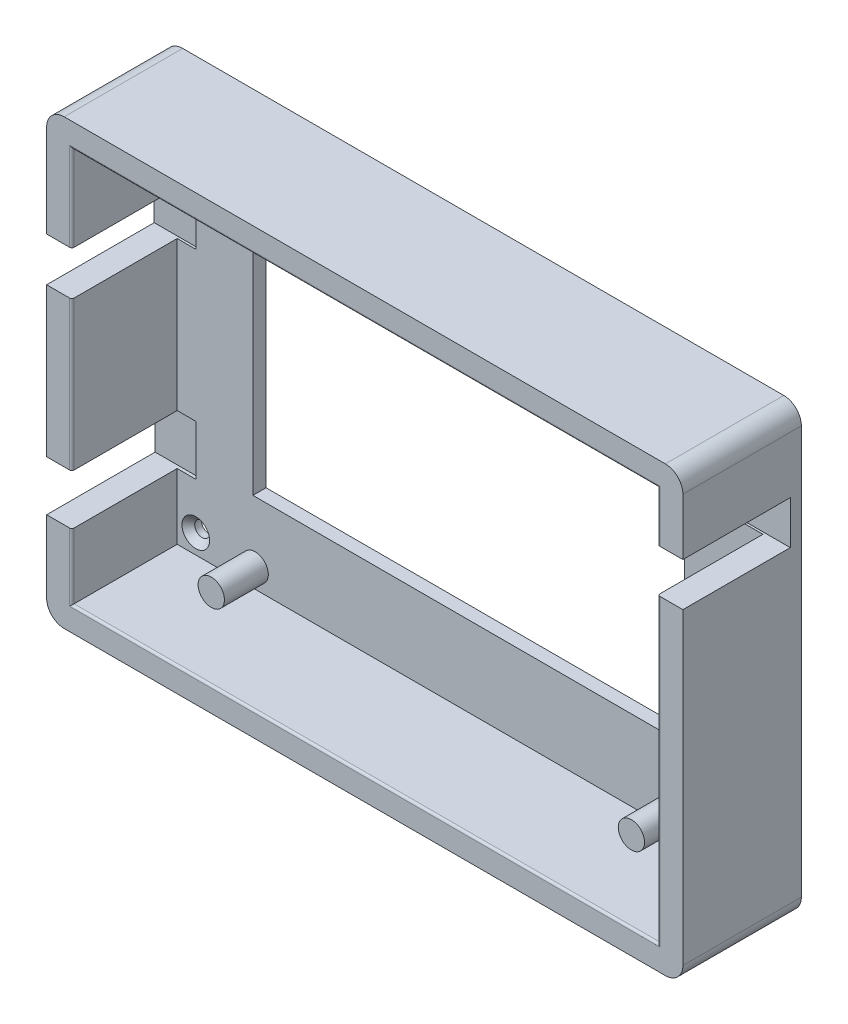
SolidWorks part; units mm, degrees
material "Caoutchouc"
ref_plane "Plan de face" through (0, 0, 0) normal (0, 0, 1) x (1, 0, 0)
ref_plane "Plan de dessus" through (0, 0, 0) normal (0, 1, 0) x (1, 0, 0)
ref_plane "Plan de droite" through (0, 0, 0) normal (1, 0, 0) x (0, 0, -1)
sketch "Esquisse1" plane through (0, 0, 0) normal (0, 0, 1) x (1, 0, 0)
  line L0 (66.75, 90) -> (66.75, 0) construction
  line L1 (0, 0) -> (133.5, 0)
  line L2 (0, 0) -> (0, 90)
  line L3 (0, 90) -> (133.5, 90)
  line L4 (133.5, 0) -> (133.5, 90)
  line L5 (0, 45) -> (133.5, 45) construction
  dimension "D1" = 133.5
  dimension "D2" = 90
sketch "EsquisseExterieur" plane through (0, 0, 0) normal (0, 0, 1) x (1, 0, 0)
  line L0 (66.75, 90) -> (66.75, 0) construction
  line L1 (-1.75, -5.5) -> (135.25, -5.5)
  line L2 (-5.75, -1.5) -> (-5.75, 91.5)
  line L3 (-1.75, 95.5) -> (135.25, 95.5)
  line L4 (139.25, -1.5) -> (139.25, 91.5)
  line L5 (-5.75, -5.5) -> (139.25, 95.5) construction
  line L6 (-5.75, 95.5) -> (139.25, -5.5) construction
  arc A0 (-1.75, -5.5) -> (-5.75, -1.5) centre (-1.75, -1.5) cw
  arc A1 (135.25, -5.5) -> (139.25, -1.5) centre (135.25, -1.5) ccw
  arc A2 (135.25, 95.5) -> (139.25, 91.5) centre (135.25, 91.5) cw
  arc A3 (-5.75, 91.5) -> (-1.75, 95.5) centre (-1.75, 91.5) cw
  point P0 (66.75, 45)
  dimension "D3" = 4
  dimension "D1" = 145
  dimension "D2" = 101
extrude "Boss.-Extru.1" add sketch "EsquisseExterieur" against normal blind 8 and the other way blind 19
extrude "Enlèv. mat.-Extru.1" cut sketch "Esquisse1" against normal blind 5 and the other way blind 47
hole_wizard "Fraisage pour vis à tête fraisée M32" positions "Esquisse6" profile "Esquisse5" countersink size "M3" standard "ISO"
sketch "Esquisse6" plane through (0, 0, -5) normal (0, 0, 1) x (1, 0, 0)
  point P0 (4.1451, 84.4434)
  point P2 (127.1274, 84.4434)
  point P4 (127.1274, 4.4159)
  point P6 (4.241, 4.4159)
sketch "Esquisse5" plane through (4.1451, 84.4434, -5) normal (1, 0, 0) x (0, -1, 0)
  line L0 (0, 0) -> (0, 6.0215)
  line L1 (0, 6.0215) -> (1.7, 5)
  line L2 (1.7, 5) -> (1.7, 1.45)
  line L3 (1.7, 1.45) -> (3.15, 0)
  line L5 (3.15, 0) -> (0, 0)
  line L6 (-1.7, 1.45) -> (-3.15, 0) construction
  line L10 (0, 6.0215) -> (-1.7, 5) construction
  line L11 (0, -6.35) -> (0, 107.95) construction
  dimension "Diamètre du perçage" = 3.4
  dimension "Profondeur du perçage" = 5
  dimension "Diamètre du fraisage entrant" = 6.3
  dimension "Angle du fraisage entrant" = 90
  dimension "Angle de pointe" = 118
sketch "Esquisse7" plane through (-5.75, 0, 0) normal (-1, 0, 0) x (0, 0, 1)
  line L0 (19, 91.5) -> (19, -1.5) construction
  line L1 (19, 70.3576) -> (-5.5113, 70.3576)
  line L2 (19, 70.3576) -> (19, 60.349)
  line L3 (19, 60.349) -> (-5.5113, 60.349)
  line L4 (-5.5113, 70.3576) -> (-5.5113, 60.349)
  point P0 (-1.0067, 57.9518)
  point P1 (-1.2778, 72.7474)
extrude "Enlèv. mat.-Extru.2" cut sketch "Esquisse7" against normal blind 10
sketch "Esquisse8" plane through (-5.75, 0, 0) normal (-1, 0, 0) x (0, 0, 1)
  line L0 (19, 60.349) -> (19, -1.5) construction
  line L1 (19, 26.3973) -> (-5.7237, 26.3973)
  line L2 (19, 26.3973) -> (19, 14.9604)
  line L3 (19, 14.9604) -> (-5.7237, 14.9604)
  line L4 (-5.7237, 26.3973) -> (-5.7237, 14.9604)
extrude "Enlèv. mat.-Extru.3" cut sketch "Esquisse8" against normal blind 10
sketch "Esquisse9" plane through (139.25, 0, 0) normal (1, 0, 0) x (0, 0, -1)
  line L0 (-19, -1.5) -> (-19, 91.5) construction
  line L1 (-19, 78.6074) -> (5.4787, 78.6074)
  line L2 (-19, 78.6074) -> (-19, 68.7301)
  line L3 (-19, 68.7301) -> (5.4787, 68.7301)
  line L4 (5.4787, 78.6074) -> (5.4787, 68.7301)
extrude "Enlèv. mat.-Extru.4" cut sketch "Esquisse9" against normal blind 10
fillet "Congé1" radius 0.5 7 edges at (133.5, 34.365, 19) (133.5, 84.3037, 19) (0, 80.1788, 19) (0, 43.3731, 19) (0, 7.4802, 19) (66.75, 0, 19) (66.75, 90, 19)
sketch "Esquisse10" plane through (0, 0, -5) normal (0, 0, 1) x (1, 0, 0)
  line L0 (4.1451, 84.4434) -> (127.1274, 84.4434) construction
  line L1 (4.241, 4.4159) -> (127.1274, 4.4159) construction
  line L2 (65.6363, 84.4434) -> (65.6842, 4.4159) construction
  line L3 (4.1451, 84.4434) -> (17.7708, 84.4434) construction
  line L4 (127.1274, 84.4434) -> (113.5135, 84.4434) construction
  line L5 (17.7708, 84.4434) -> (17.7708, 4.4159) construction
  line L6 (113.5135, 84.4434) -> (113.5135, 4.4159) construction
  circle A0 centre (17.7708, 84.4434) radius 3
  circle A1 centre (113.5135, 84.4434) radius 3
  circle A2 centre (17.7708, 4.4159) radius 3
  circle A3 centre (113.5135, 4.4159) radius 3
extrude "Boss.-Extru.2" add sketch "Esquisse10" along normal blind 10
sketch "Esquisse12" plane through (0, 0, -5) normal (0, 0, 1) x (1, 0, 0)
  line L1 (17.2545, 73.4599) -> (115.6632, 73.4599)
  line L2 (17.2545, 73.4599) -> (17.2545, 18.287)
  line L3 (17.2545, 18.287) -> (115.6632, 18.287)
  line L4 (115.6632, 73.4599) -> (115.6632, 18.287)
extrude "Enlèv. mat.-Extru.5" cut sketch "Esquisse12" against normal blind 10
